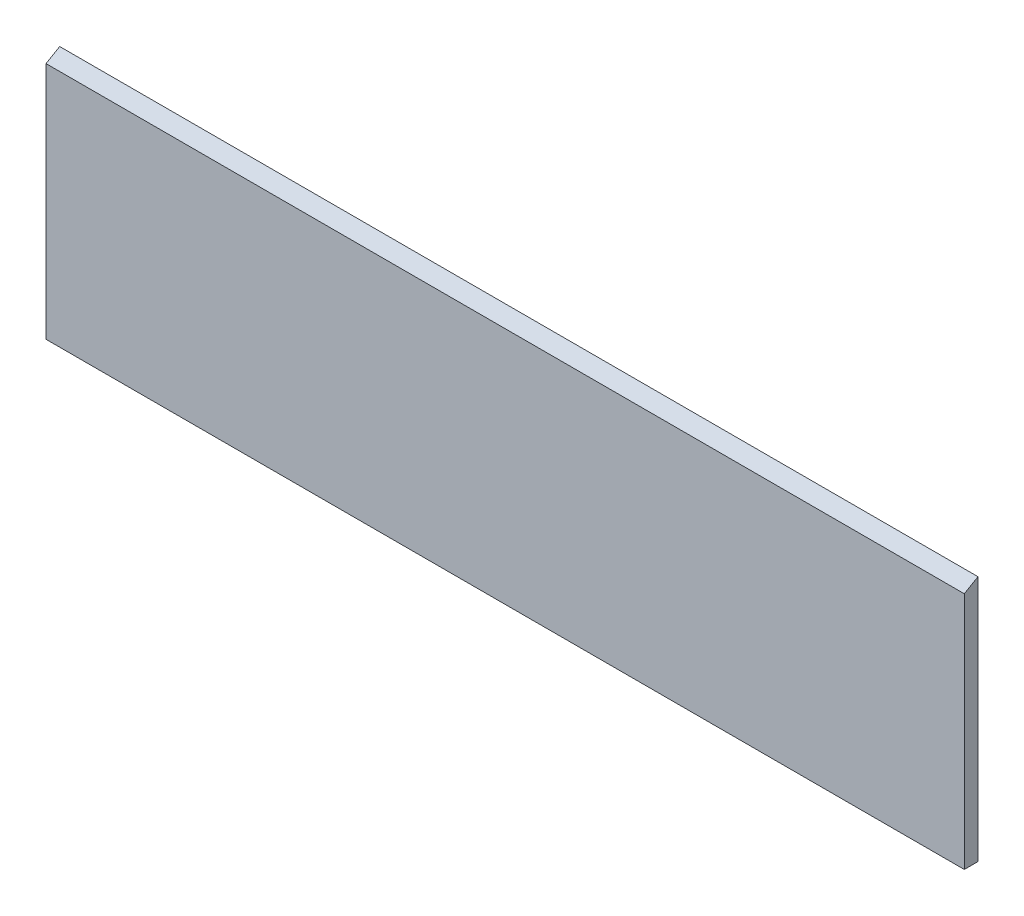
SolidWorks part; units mm, degrees
ref_plane "Front Plane" through (0, 0, 0) normal (0, 0, 1) x (1, 0, 0)
ref_plane "Top Plane" through (0, 0, 0) normal (0, 1, 0) x (1, 0, 0)
ref_plane "Right Plane" through (0, 0, 0) normal (1, 0, 0) x (0, 0, -1)
sketch "Sketch1" plane through (0, 0, 0) normal (0, 0, 1) x (1, 0, 0)
  line L1 (0, 0) -> (670, 0)
  line L2 (0, 0) -> (0, 180)
  line L3 (0, 180) -> (670, 180)
  line L4 (670, 0) -> (670, 180)
  dimension "D1" = 180
  dimension "D2" = 670
extrude "Extrude1" add sketch "Sketch1" along normal blind 10
sketch "Sketch2" plane through (670, 0, 0) normal (1, 0, 0) x (0, 0, -1)
  line L0 (0, 180) -> (-10, 174.2265)
  line L1 (-10, 0) -> (-10, 180) construction
  line L2 (-10, 174.2265) -> (-10, 180)
  line L3 (-10, 180) -> (0, 180)
  dimension "D1" = 60
extrude "Extrude2" cut sketch "Sketch2" against normal through all
